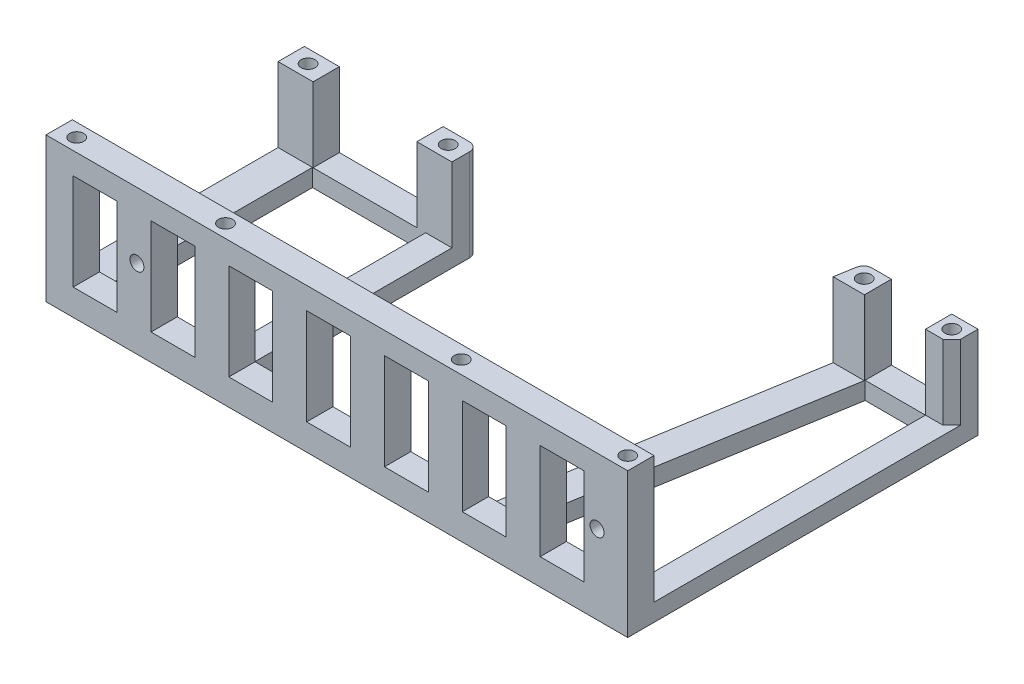
SolidWorks part; units mm, degrees
ref_plane "Спереди" through (0, 0, 0) normal (0, 0, 1) x (1, 0, 0)
ref_plane "Сверху" through (0, 0, 0) normal (0, 1, 0) x (1, 0, 0)
ref_plane "Справа" through (0, 0, 0) normal (1, 0, 0) x (0, 0, -1)
sketch "Эскиз1" plane through (0, 0, 0) normal (0, 1, 0) x (1, 0, 0)
  line L0 (-63, 0) -> (63, 0) construction
  line L1 (63, 0) -> (63, 21) construction
  line L2 (66, 24) -> (66, -56)
  line L3 (66, -56) -> (-66.85, -56)
  line L4 (-66.85, -56) -> (-66.85, 3)
  line L5 (-66.85, 3) -> (-59.15, 3)
  line L6 (-59, -3) -> (-59, -50)
  line L7 (-31, 3) -> (-31, -56) construction
  line L9 (60, 24) -> (66, 24)
  line L10 (-63, 3) -> (-63, -56) construction
  line L11 (63, 24) -> (63, -56) construction
  line L12 (-33.15, -50) -> (-33.15, -3)
  line L13 (-34.85, 3) -> (-27.15, 3)
  line L14 (-27.15, 3) -> (-27.15, -50)
  line L15 (-59, -50) -> (-33.15, -50)
  line L16 (60, 18) -> (60, -50)
  line L17 (-59.15, 3) -> (-34.85, 3)
  line L18 (-59, -3) -> (-33.15, -3)
  line L19 (63, 21) -> (43, 21) construction
  line L20 (60, 24) -> (40.1333, 24)
  line L21 (40.1333, 24) -> (27.7042, -50)
  line L22 (60, 18) -> (46.2236, 18)
  line L23 (46.2236, 18) -> (34.8023, -50)
  line L24 (-27.15, -50) -> (27.7042, -50)
  line L25 (34.8023, -50) -> (60, -50)
  circle A0 centre (63, 21) radius 1.6
  circle A1 centre (-63, 0) radius 1.6
  circle A2 centre (-31, 0) radius 1.6
  circle A3 centre (43, 21) radius 1.6
  point P2 (0, 0)
  point P19 (-31, 0)
  dimension "D9" = 32
  dimension "D10" = 6
  dimension "D12" = 7
  dimension "D2" = 6
  dimension "D3" = 126
  dimension "D4" = 21
  dimension "D5" = 80
  dimension "D6" = 32
  dimension "D7" = 3
  dimension "D8" = 3
  dimension "D11" = 6
  dimension "D13" = 6
  dimension "D14" = 7.85
  dimension "D15" = 6
  dimension "D16" = 3.85
  dimension "D17" = 6
  dimension "D18" = 6
  dimension "D19" = 6
extrude "Бобышка-Вытянуть1" add sketch "Эскиз1" along normal blind 4
sketch "Эскиз2" plane through (0, 4, 0) normal (0, -1, 0) x (1, 0, 0)
  line L0 (-27.15, -3) -> (-66.85, -3) construction
  line L1 (-66.85, 3) -> (-58.85, 3)
  line L2 (-66.85, 3) -> (-66.85, -3)
  line L3 (-66.85, -3) -> (-58.85, -3)
  line L4 (-58.85, 3) -> (-58.85, -3)
  line L5 (-66.85, -3) -> (-66.85, 56) construction
  line L7 (66, -20) -> (66, -24)
  line L8 (60, -18) -> (60, -24)
  line L9 (60, -24) -> (66, -24)
  line L10 (64, -18) -> (60, -18)
  line L11 (60, -18) -> (66, -24) construction
  line L13 (-35.15, 3) -> (-27.15, 3)
  line L14 (-35.15, 3) -> (-35.15, -3)
  line L15 (-35.15, -3) -> (-27.15, -3)
  line L16 (-27.15, 3) -> (-27.15, -3)
  line L19 (46.2236, -18) -> (46.2236, -24)
  line L20 (66, -24) -> (40.1333, -24) construction
  line L21 (46.2236, -24) -> (40.1333, -24)
  line L22 (66, -20) -> (64, -18)
  line L23 (40.1333, -24) -> (27.7042, 50) construction
  line L25 (46.1951, -17.8307) -> (39.0971, -17.8307)
  line L26 (46.2236, -18) -> (34.8023, 50) construction
  line L27 (39.0971, -17.8307) -> (40.1333, -24)
  line L28 (46.1951, -17.8307) -> (46.2236, -18)
  circle A0 centre (63, -21) radius 1.6
  circle A1 centre (-63, 0) radius 1.6
  circle A2 centre (-31, 0) radius 1.6
  circle A3 centre (43, -21) radius 1.6
  point P0 (-63, 0)
  point P7 (63, -21)
  point P18 (-31, 0)
  point P44 (-66.85, 0)
  dimension "D1" = 6
  dimension "D2" = 8
  dimension "D3" = 8
  dimension "D4" = 4
extrude "Бобышка-Вытянуть2" add sketch "Эскиз2" against normal blind 17
fillet "Скругление1" radius 2 2 edges at (-27.15, 10.5, -3) (40.1333, 10.5, -24)
sketch "Эскиз3" plane through (0, 4, 0) normal (0, -1, 0) x (1, 0, 0)
  line L0 (-66.85, 56) -> (66, 56)
  line L1 (66, 56) -> (66, 50)
  line L2 (66, 56) -> (66, -24) construction
  line L3 (66, 50) -> (-66.85, 50)
  line L4 (-66.85, -3) -> (-66.85, 56) construction
  line L5 (-66.85, 50) -> (-66.85, 56)
  line L6 (27.7042, 50) -> (-27.15, 50) construction
  point P4 (-0.425, 50)
extrude "Бобышка-Вытянуть3" add sketch "Эскиз3" against normal blind 29
sketch "Эскиз4" plane through (0, 0, 50) normal (0, 0, -1) x (-1, 0, 0)
  line L1 (15.0953, 6) -> (25.0953, 6)
  line L2 (15.0953, 6) -> (15.0953, 28)
  line L3 (15.0953, 28) -> (25.0953, 28)
  line L4 (25.0953, 6) -> (25.0953, 28)
  line L5 (15.0953, 6) -> (25.0953, 28) construction
  line L6 (15.0953, 28) -> (25.0953, 6) construction
  line L7 (20.0953, 17) -> (2.3215, 17) construction
  line L8 (-2.6785, 6) -> (7.3215, 6)
  line L9 (-2.6785, 6) -> (-2.6785, 28)
  line L10 (-2.6785, 28) -> (7.3215, 28)
  line L11 (7.3215, 6) -> (7.3215, 28)
  line L12 (-2.6785, 6) -> (7.3215, 28) construction
  line L13 (-2.6785, 28) -> (7.3215, 6) construction
  line L14 (-20.4523, 6) -> (-10.4523, 6)
  line L15 (-20.4523, 6) -> (-20.4523, 28)
  line L16 (-20.4523, 28) -> (-10.4523, 28)
  line L17 (-10.4523, 6) -> (-10.4523, 28)
  line L18 (-20.4523, 6) -> (-10.4523, 28) construction
  line L19 (-20.4523, 28) -> (-10.4523, 6) construction
  line L20 (-38.2262, 6) -> (-28.2262, 6)
  line L21 (-38.2262, 6) -> (-38.2262, 28)
  line L22 (-38.2262, 28) -> (-28.2262, 28)
  line L23 (-28.2262, 6) -> (-28.2262, 28)
  line L24 (-38.2262, 6) -> (-28.2262, 28) construction
  line L25 (-38.2262, 28) -> (-28.2262, 6) construction
  line L26 (-56, 6) -> (-46, 6)
  line L27 (-56, 6) -> (-56, 28)
  line L28 (-56, 28) -> (-46, 28)
  line L29 (-46, 6) -> (-46, 28)
  line L30 (-56, 6) -> (-46, 28) construction
  line L31 (-56, 28) -> (-46, 6) construction
  line L32 (2.3215, 17) -> (-15.4523, 17) construction
  line L33 (-15.4523, 17) -> (-33.2262, 17) construction
  line L34 (-33.2262, 17) -> (-51, 17) construction
  line L35 (55.643, 17) -> (37.8692, 17) construction
  line L36 (32.8692, 6) -> (42.8692, 6)
  line L37 (32.8692, 6) -> (32.8692, 28)
  line L38 (32.8692, 28) -> (42.8692, 28)
  line L39 (42.8692, 6) -> (42.8692, 28)
  line L40 (32.8692, 6) -> (42.8692, 28) construction
  line L41 (32.8692, 28) -> (42.8692, 6) construction
  line L42 (50.643, 6) -> (60.643, 6)
  line L43 (50.643, 6) -> (50.643, 28)
  line L44 (50.643, 28) -> (60.643, 28)
  line L45 (60.643, 6) -> (60.643, 28)
  line L46 (50.643, 6) -> (60.643, 28) construction
  line L47 (50.643, 28) -> (60.643, 6) construction
  line L48 (37.8692, 17) -> (20.0953, 17) construction
  line L49 (20.0953, 17) -> (2.3215, 17) construction
  line L50 (66.85, 17) -> (-66, 17) construction
  line L55 (66.85, 33) -> (-66, 33) construction
  point P0 (20.0953, 17)
  point P7 (2.3215, 17)
  point P12 (-15.4523, 17)
  point P17 (-56.0042, -33.1117)
  point P22 (-51, 17)
  point P29 (37.8692, 17)
  point P37 (55.643, 17)
  dimension "D1" = 10
  dimension "D2" = 22
  dimension "D3" = 15
  dimension "D4" = 16
extrude "Вырез-Вытянуть1" cut sketch "Эскиз4" against normal through all
sketch "Эскиз5" plane through (0, 0, 0) normal (0, 1, 0) x (1, 0, 0)
  line L0 (-66.85, -53) -> (66, -53) construction
  line L1 (-66.85, -3) -> (-66.85, -50) construction
  line L2 (66, -50) -> (66, 20) construction
  line L3 (-66.85, -56) -> (66, -56) construction
  circle A0 centre (-62.85, -53) radius 1.6
  circle A1 centre (-28.85, -53) radius 1.6
  circle A2 centre (63, -53) radius 1.6
  circle A3 centre (25, -53) radius 1.6
  dimension "D2" = 34
  dimension "D1" = 3
  dimension "D3" = 4
  dimension "D4" = 38
  dimension "D5" = 3
extrude "Вырез-Вытянуть2" cut sketch "Эскиз5" along normal through all
sketch "Эскиз6" plane through (0, 0, 50) normal (0, 0, -1) x (-1, 0, 0)
  line L0 (46.08, 4) -> (46.08, 33) construction
  line L2 (66.85, 33) -> (-66, 33) construction
  line L3 (-59, 4) -> (-59, 33) construction
  line L4 (-34.8023, 4) -> (-27.7042, 4) construction
  line L7 (-66, 33) -> (-66, 4) construction
  circle A0 centre (46.08, 18) radius 1.6
  circle A1 centre (-59, 18) radius 1.6
  point P16 (0, 0)
  point P17 (0, 0)
  dimension "D1" = 15
  dimension "D2" = 15
  dimension "D3" = 7
  dimension "D4" = 105.08
extrude "Вырез-Вытянуть3" cut sketch "Эскиз6" against normal through all
